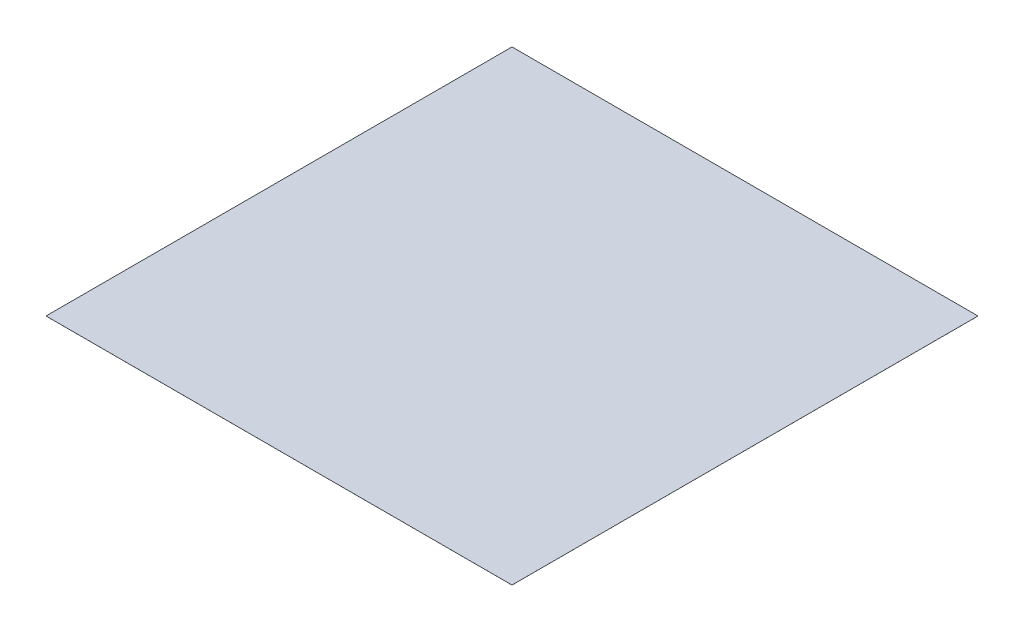
SolidWorks part; units mm, degrees
ref_plane "Front Plane" through (0, 0, 0) normal (0, 0, 1) x (1, 0, 0)
ref_plane "Top Plane" through (0, 0, 0) normal (0, 1, 0) x (1, 0, 0)
ref_plane "Right Plane" through (0, 0, 0) normal (1, 0, 0) x (0, 0, -1)
sketch "Sketch2" plane through (0, 0, 0) normal (0, 1, 0) x (1, 0, 0)
  line L1 (-125000, 125000) -> (125000, 125000)
  line L2 (-125000, 125000) -> (-125000, -125000)
  line L3 (-125000, -125000) -> (125000, -125000)
  line L4 (125000, 125000) -> (125000, -125000)
  line L5 (-125000, 125000) -> (125000, -125000) construction
  line L6 (-125000, -125000) -> (125000, 125000) construction
  point P0 (0, 0)
  dimension "D1" = 250000
  dimension "D2" = 250000
extrude "Boss-Extrude1" add sketch "Sketch2" along normal blind 10
